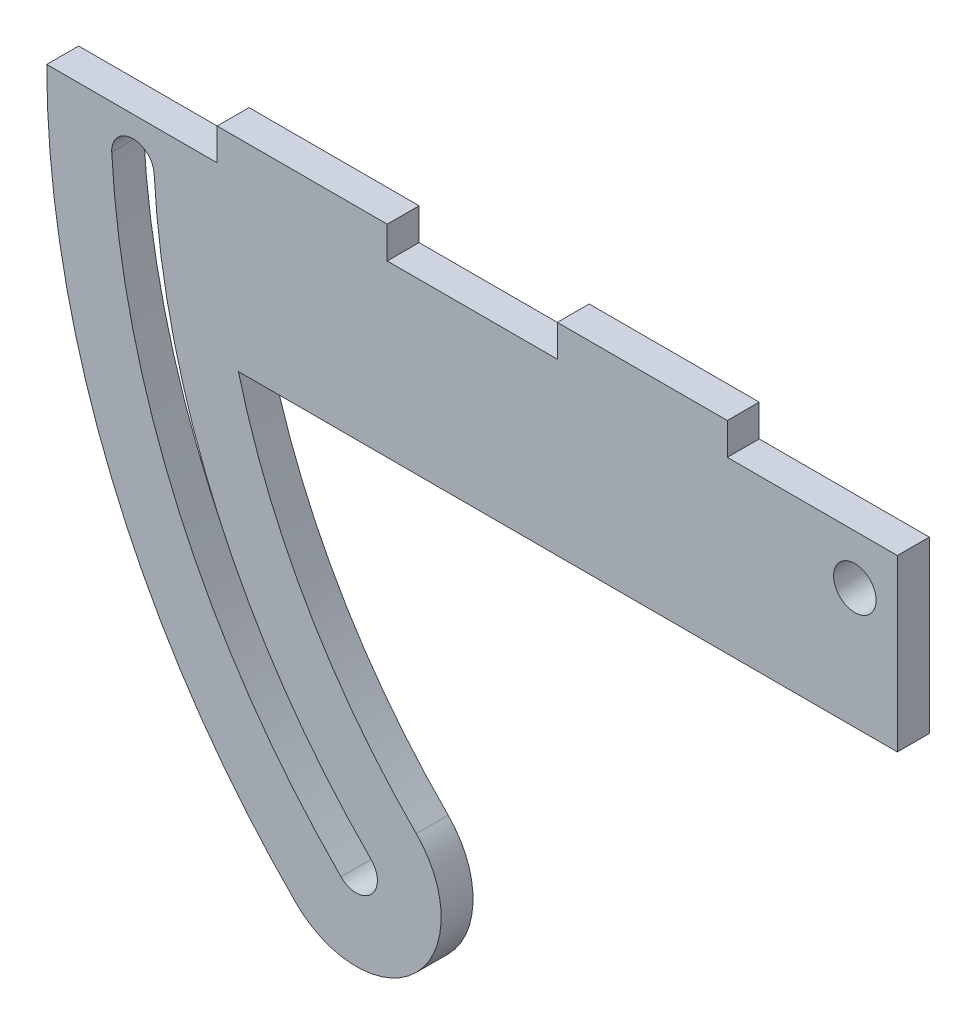
SolidWorks part; units mm, degrees
ref_plane "Front Plane" through (0, 0, 0) normal (0, 0, 1) x (1, 0, 0)
ref_plane "Top Plane" through (0, 0, 0) normal (0, 1, 0) x (1, 0, 0)
ref_plane "Right Plane" through (0, 0, 0) normal (1, 0, 0) x (0, 0, -1)
sketch "Sketch1" plane through (0, 0, 0) normal (0, 0, 1) x (1, 0, 0)
  line L0 (50.8, 26.4332) -> (76.2, 26.4332)
  line L1 (28.5752, 1.02) -> (127, 1.02)
  line L2 (101.6, 26.4332) -> (127, 26.4332)
  line L3 (-0.0527, 26.4332) -> (25.4, 26.4332)
  line L4 (127, 1.02) -> (127, 26.4332)
  line L5 (76.2, 26.4332) -> (76.2, 31.1957)
  line L6 (25.4, 26.4332) -> (25.4, 31.1957)
  line L7 (25.4, 31.1957) -> (50.8, 31.1957)
  line L8 (50.8, 26.4332) -> (50.8, 31.1957)
  line L9 (101.6, 31.1957) -> (76.2, 31.1957)
  line L10 (101.6, 26.4332) -> (101.6, 31.1957)
  circle A0 centre (120.65, 19.05) radius 3.175
  arc A1 (-0.0527, 26.4332) -> (37.1805, -63.4269) centre (127, 26.4332) ccw
  arc A2 (28.5752, 1.02) -> (55.141, -45.4664) centre (127, 26.4332) ccw
  arc A3 (55.141, -45.4664) -> (37.1805, -63.4269) centre (46.1607, -54.4467) cw
  arc A4 (15.9951, 20.2342) -> (9.652, 19.939) centre (12.8236, 20.0866) ccw
  arc A5 (9.652, 19.939) -> (43.8955, -56.6714) centre (127, 26.4332) ccw
  arc A6 (15.9951, 20.2342) -> (48.3854, -52.1814) centre (127, 26.4332) ccw
  arc A7 (48.3854, -52.1814) -> (43.8955, -56.6714) centre (46.1607, -54.4467) cw
  dimension "D2" = 25.4
  dimension "D3" = 4.7625
extrude "Boss-Extrude1" add sketch "Sketch1" along normal blind 4.7625
